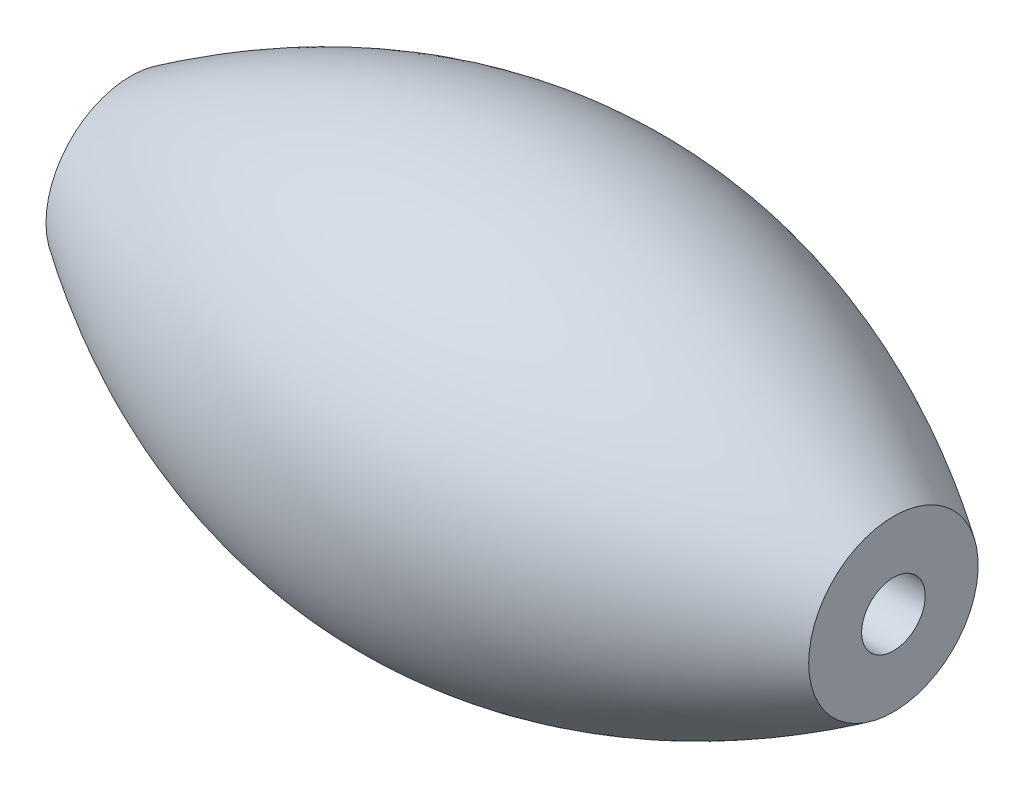
SolidWorks part; units mm, degrees
ref_plane "前视基准面" through (0, 0, 0) normal (0, 0, 1) x (1, 0, 0)
ref_plane "上视基准面" through (0, 0, 0) normal (0, 1, 0) x (1, 0, 0)
ref_plane "右视基准面" through (0, 0, 0) normal (1, 0, 0) x (0, 0, -1)
sketch "草图1" plane through (0, 0, 0) normal (0, 0, 1) x (1, 0, 0)
  line L0 (-37.6575, 0) -> (-1.6575, 0) construction
  line L1 (-1.6575, 0) -> (-1.6575, 4)
  line L2 (-37.6575, 0) -> (-1.6575, 0)
  line L3 (-37.6575, 4) -> (-37.6575, 0)
  line L4 (-19.6575, 0) -> (-19.6575, 10) construction
  spline S0 degree 2 poles (-1.6575, 4) (-19.6575, 16) (-37.6575, 4) knots 0 0 0 1 1 1
  dimension "D1" = 4
  dimension "D2" = 10
revolve "旋转1" add sketch "草图1" angle 360 about L2
sketch "草图2" plane through (-1.6575, 0, 0) normal (1, 0, 0) x (0, 0, -1)
  circle A0 centre (0, 0) radius 1.5
  dimension "D1" = 3
extrude "切除-拉伸1" cut sketch "草图2" against normal blind 45
